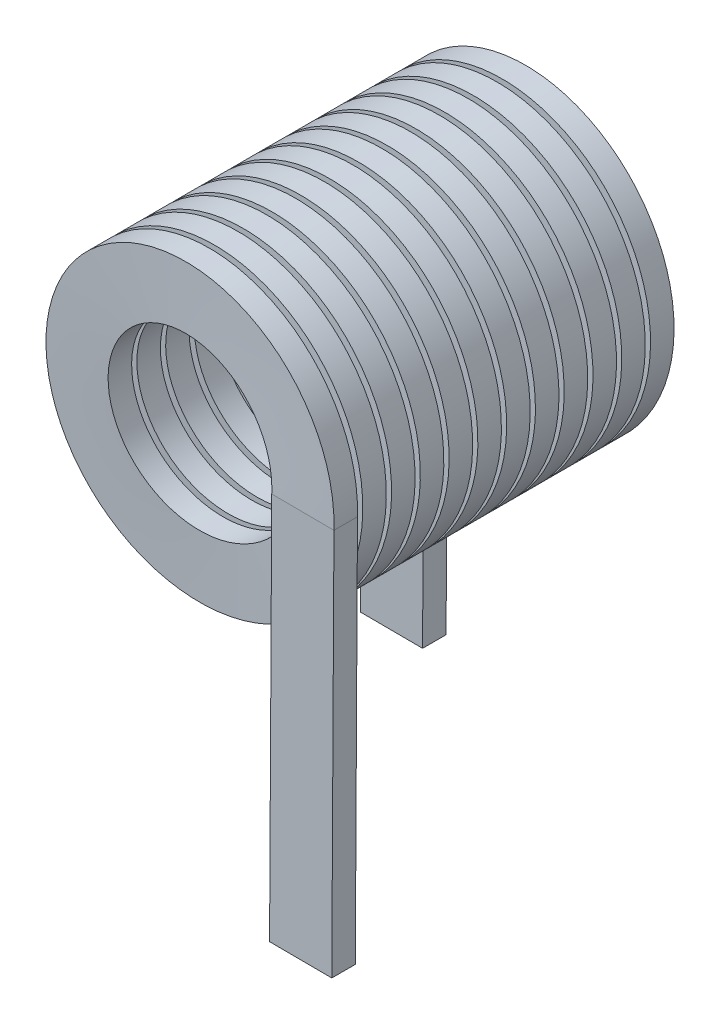
SolidWorks part; units mm, degrees
ref_plane "Front Plane" through (0, 0, 0) normal (0, 0, 1) x (1, 0, 0)
ref_plane "Top Plane" through (0, 0, 0) normal (0, 1, 0) x (1, 0, 0)
ref_plane "Right Plane" through (0, 0, 0) normal (1, 0, 0) x (0, 0, -1)
sketch "Sketch1" plane through (0, 0, 0) normal (0, 0, 1) x (1, 0, 0)
  circle A0 centre (0, 0) radius 15.6845
  dimension "D1" = 31.369
curve "Helix/Spiral1" pitch 3.7592 height 43.2308 turns 11.5
sketch "Sketch6" plane through (0, 0, 0) normal (1, 0, 0) x (0, 0, -1)
  line L0 (-11.0007, 0) -> (53.4115, 0) construction
sketch3d "3DSketch4"
  line L0 (19.7482, 0.0879, 41.6907) -> (19.7482, 0.0879, 44.7641)
  line L1 (19.7482, 0.0879, 44.7641) -> (11.6202, 0.0879, 44.7641)
  line L2 (11.6202, 0.0879, 44.7641) -> (11.6202, 0.0879, 41.6907)
  line L3 (11.6202, 0.0879, 41.6907) -> (19.7482, 0.0879, 41.6907)
  line L4 (15.6842, 0.0879, 43.2274) -> (15.6842, 0.0879, 39.0048) construction
  line L5 (15.6842, 0.0879, 43.2274) -> (20.225, 0.0879, 43.2274) construction
  spline S0 degree 3 poles (-15.6845, 0, 0) (-15.6845, 1.8694, 0.0713) (-15.0016, 5.6424, 0.2153) (-12.0593, 10.5536, 0.4301) (-7.5753, 14.1229, 0.6452) (-2.1228, 15.8847, 0.8603) (3.601, 15.6162, 1.0754) (8.8645, 13.3511, 1.2905) (12.9947, 9.3793, 1.5056) (15.4636, 4.2083, 1.7206) (15.9556, -1.5007, 1.9357) (14.4077, -7.0178, 2.1508) (11.0179, -11.6378, 2.3659) (6.2195, -14.7699, 2.5809) (0.626, -16.0137, 2.796) (-5.0475, -15.2103, 3.0111) (-10.0757, -12.4624, 3.2262) (-13.8159, -8.1212, 3.4413) (-15.7897, -2.7418, 3.6563) (-15.7449, 2.9882, 3.8714) (-13.6872, 8.3361, 4.0865) (-9.8797, 12.6184, 4.3016) (-4.8091, 15.2874, 4.5167) (0.8763, 16.002, 4.7317) (6.4496, 14.6709, 4.9468) (11.1985, 11.4641, 5.1619) (14.5156, 6.7918, 5.377) (15.9771, 1.2511, 5.592) (15.3959, -4.4495, 5.8071) (12.8465, -9.5812, 6.0222) (8.6547, -13.4881, 6.2373) (3.3565, -15.6705, 6.4524) (-2.3709, -15.8496, 6.6674) (-7.7951, -14.0024, 6.8825) (-12.2228, -10.3651, 7.0976) (-15.0878, -5.4027, 7.3127) (-16.024, 0.2505, 7.5278) (-14.9116, 5.8716, 7.7428) (-11.8928, 10.7421, 7.9579) (-7.3536, 14.2392, 8.173) (-1.8743, 15.916, 8.3881) (3.8446, 15.558, 8.6031) (9.072, 13.211, 8.8182) (13.1397, 9.175, 9.0333) (15.5275, 3.9661, 9.2484) (15.9301, -1.7499, 9.4635) (14.2963, -7.2421, 9.6785) (10.8347, -11.8085, 9.8936) (5.9879, -14.8653, 10.1087) (0.3757, -16.0216, 10.3238) (-5.2846, -15.1296, 10.5389) (-10.2693, -12.3034, 10.7539) (-13.9411, -7.9043, 10.969) (-15.8306, -2.4946, 11.1841) (-15.6963, 3.2339, 11.3992) (-13.5553, 8.549, 11.6142) (-9.6813, 12.7712, 11.8293) (-4.5696, 15.3607, 12.0444) (1.1262, 15.9863, 12.2595) (6.6781, 14.5683, 12.4746) (11.3763, 11.2877, 12.6896) (14.62, 6.5641, 12.9047) (15.9947, 1.0013, 13.1198) (15.3245, -4.6895, 13.3349) (12.6952, -9.7808, 13.55) (8.4428, -13.6217, 13.765) (3.1112, -15.7211, 13.9801) (-2.6183, -15.8106, 14.1952) (-8.013, -13.8789, 14.4103) (-12.3833, -10.1728, 14.6253) (-15.1704, -5.1662, 14.8404) (-16.0181, 0.5009, 15.0555) (-14.818, 6.1039, 15.2706) (-11.7235, 10.9266, 15.4857) (-7.1302, 14.3524, 15.7007) (-1.6253, 15.9433, 15.9158) (4.0873, 15.496, 16.1309) (9.2774, 13.0676, 16.346) (13.2815, 8.9685, 16.5611) (15.5875, 3.7229, 16.7761) (15.9009, -1.9986, 16.9912) (14.1813, -7.4647, 17.2063) (10.6488, -11.9764, 17.4214) (5.7549, -14.957, 17.6364) (0.1252, -16.0255, 17.8515) (-5.5204, -15.0452, 18.0666) (-10.4603, -12.1414, 18.2817) (-14.0629, -7.6854, 18.4968) (-15.8677, -2.2469, 18.7118) (-15.6438, 3.4788, 18.9269) (-13.42, 8.7599, 19.142) (-9.4805, 12.921, 19.3571) (-4.329, 15.4302, 19.5722) (1.376, 15.9668, 19.7872) (6.905, 14.4621, 20.0023) (11.5513, 11.1085, 20.2174) (14.7208, 6.3348, 20.4325) (16.0084, 0.7512, 20.6475) (15.2493, -4.9285, 20.8626) (12.5408, -9.978, 21.0777) (8.2289, -13.752, 21.2928) (2.8651, -15.7678, 21.5079) (-2.8651, -15.7678, 21.7229) (-8.2289, -13.752, 21.938) (-12.5408, -9.978, 22.1531) (-15.2493, -4.9285, 22.3682) (-16.0084, 0.7512, 22.5833) (-14.7208, 6.3348, 22.7983) (-11.5513, 11.1085, 23.0134) (-6.905, 14.4621, 23.2285) (-1.376, 15.9668, 23.4436) (4.329, 15.4302, 23.6586) (9.4805, 12.921, 23.8737) (13.42, 8.7599, 24.0888) (15.6438, 3.4788, 24.3039) (15.8677, -2.2469, 24.519) (14.0629, -7.6854, 24.734) (10.4603, -12.1414, 24.9491) (5.5204, -15.0452, 25.1642) (-0.1252, -16.0255, 25.3793) (-5.7549, -14.957, 25.5944) (-10.6488, -11.9764, 25.8094) (-14.1813, -7.4647, 26.0245) (-15.9009, -1.9986, 26.2396) (-15.5875, 3.7229, 26.4547) (-13.2815, 8.9685, 26.6697) (-9.2774, 13.0676, 26.8848) (-4.0873, 15.496, 27.0999) (1.6253, 15.9433, 27.315) (7.1302, 14.3524, 27.5301) (11.7235, 10.9266, 27.7451) (14.818, 6.1039, 27.9602) (16.0181, 0.5009, 28.1753) (15.1704, -5.1662, 28.3904) (12.3833, -10.1728, 28.6055) (8.013, -13.8789, 28.8205) (2.6183, -15.8106, 29.0356) (-3.1112, -15.7211, 29.2507) (-8.4428, -13.6217, 29.4658) (-12.6952, -9.7808, 29.6808) (-15.3245, -4.6895, 29.8959) (-15.9947, 1.0013, 30.111) (-14.62, 6.5641, 30.3261) (-11.3763, 11.2877, 30.5412) (-6.6781, 14.5683, 30.7562) (-1.1262, 15.9863, 30.9713) (4.5696, 15.3607, 31.1864) (9.6813, 12.7712, 31.4015) (13.5553, 8.549, 31.6166) (15.6963, 3.2339, 31.8316) (15.8306, -2.4946, 32.0467) (13.9411, -7.9043, 32.2618) (10.2693, -12.3034, 32.4769) (5.2846, -15.1296, 32.6919) (-0.3757, -16.0216, 32.907) (-5.9879, -14.8653, 33.1221) (-10.8347, -11.8085, 33.3372) (-14.2963, -7.2421, 33.5523) (-15.9301, -1.7499, 33.7673) (-15.5275, 3.9661, 33.9824) (-13.1397, 9.175, 34.1975) (-9.072, 13.211, 34.4126) (-3.8446, 15.558, 34.6277) (1.8743, 15.916, 34.8427) (7.3536, 14.2392, 35.0578) (11.8928, 10.7421, 35.2729) (14.9116, 5.8716, 35.488) (16.024, 0.2505, 35.703) (15.0878, -5.4027, 35.9181) (12.2228, -10.3651, 36.1332) (7.7951, -14.0024, 36.3483) (2.3709, -15.8496, 36.5634) (-3.3565, -15.6705, 36.7784) (-8.6547, -13.4881, 36.9935) (-12.8465, -9.5812, 37.2086) (-15.3959, -4.4495, 37.4237) (-15.9771, 1.2511, 37.6388) (-14.5156, 6.7918, 37.8538) (-11.1985, 11.4641, 38.0689) (-6.4496, 14.6709, 38.284) (-0.8763, 16.002, 38.4991) (4.8091, 15.2874, 38.7141) (9.8797, 12.6184, 38.9292) (13.6872, 8.3361, 39.1443) (15.7449, 2.9882, 39.3594) (15.7897, -2.7418, 39.5745) (13.8159, -8.1212, 39.7895) (10.0757, -12.4624, 40.0046) (5.0475, -15.2103, 40.2197) (-0.626, -16.0137, 40.4348) (-6.2195, -14.7699, 40.6499) (-11.0179, -11.6378, 40.8649) (-14.4077, -7.0178, 41.08) (-15.9556, -1.5007, 41.2951) (-15.4636, 4.2083, 41.5102) (-12.9947, 9.3793, 41.7252) (-8.8645, 13.3511, 41.9403) (-3.601, 15.6162, 42.1554) (2.1228, 15.8847, 42.3705) (7.5753, 14.1229, 42.5856) (12.0593, 10.5536, 42.8007) (15.0016, 5.6424, 43.0155) (15.6845, 1.8694, 43.1595) (15.6845, 0, 43.2308) knots 0 0 0 0 0.004975 0.00995 0.014925 0.0199 0.024876 0.029851 0.034826 0.039801 0.044776 0.049751 0.054726 0.059701 0.064677 0.069652 0.074627 0.079602 0.084577 0.089552 0.094527 0.099502 0.104478 0.109453 0.114428 0.119403 0.124378 0.129353 0.134328 0.139303 0.144279 0.149254 0.154229 0.159204 0.164179 0.169154 0.174129 0.179104 0.18408 0.189055 0.19403 0.199005 0.20398 0.208955 0.21393 0.218905 0.223881 0.228856 0.233831 0.238806 0.243781 0.248756 0.253731 0.258706 0.263682 0.268657 0.273632 0.278607 0.283582 0.288557 0.293532 0.298507 0.303483 0.308458 0.313433 0.318408 0.323383 0.328358 0.333333 0.338308 0.343284 0.348259 0.353234 0.358209 0.363184 0.368159 0.373134 0.378109 0.383085 0.38806 0.393035 0.39801 0.402985 0.40796 0.412935 0.41791 0.422886 0.427861 0.432836 0.437811 0.442786 0.447761 0.452736 0.457711 0.462687 0.467662 0.472637 0.477612 0.482587 0.487562 0.492537 0.497512 0.502488 0.507463 0.512438 0.517413 0.522388 0.527363 0.532338 0.537313 0.542289 0.547264 0.552239 0.557214 0.562189 0.567164 0.572139 0.577114 0.58209 0.587065 0.59204 0.597015 0.60199 0.606965 0.61194 0.616915 0.621891 0.626866 0.631841 0.636816 0.641791 0.646766 0.651741 0.656716 0.661692 0.666667 0.671642 0.676617 0.681592 0.686567 0.691542 0.696517 0.701493 0.706468 0.711443 0.716418 0.721393 0.726368 0.731343 0.736318 0.741294 0.746269 0.751244 0.756219 0.761194 0.766169 0.771144 0.776119 0.781095 0.78607 0.791045 0.79602 0.800995 0.80597 0.810945 0.81592 0.820896 0.825871 0.830846 0.835821 0.840796 0.845771 0.850746 0.855721 0.860697 0.865672 0.870647 0.875622 0.880597 0.885572 0.890547 0.895522 0.900498 0.905473 0.910448 0.915423 0.920398 0.925373 0.930348 0.935323 0.940299 0.945274 0.950249 0.955224 0.960199 0.965174 0.970149 0.975124 0.9801 0.985075 0.99005 0.995025 1 1 1 1 construction
  dimension "D1" = 3.0734
  dimension "D2" = 8.128
sweep "Sweep2" add profiles "3DSketch4" path "Helix/Spiral1"
sketch "Sketch3" plane through (-0.0005, -0.0879, 0) normal (-0.0056, -1, 0) x (1, -0.0056, 0)
  line L4 (-19.7482, -1.5367) -> (-11.6202, -1.5367)
  line L5 (-19.7482, 1.5367) -> (-19.7482, -1.5367)
  line L6 (-11.6202, 1.5367) -> (-19.7482, 1.5367)
  line L7 (-11.6202, -1.5367) -> (-11.6202, 1.5367)
  line L8 (-19.7482, -1.5367) -> (-11.6202, -1.5367)
  line L9 (-19.7482, 1.5367) -> (-19.7482, -1.5367)
  line L10 (-11.6202, 1.5367) -> (-19.7482, 1.5367)
  line L11 (-11.6202, -1.5367) -> (-11.6202, 1.5367)
  dimension "D1" = 0
extrude "Boss-Extrude1" add sketch "Sketch3" along normal blind 50.8
sketch "Sketch4" plane through (0.0005, 0.0879, 0) normal (-0.0056, -1, 0) x (1, -0.0056, 0)
  line L4 (11.6202, 41.6941) -> (19.7482, 41.6941)
  line L5 (11.6202, 44.7675) -> (11.6202, 41.6941)
  line L6 (19.7482, 44.7675) -> (11.6202, 44.7675)
  line L7 (19.7482, 41.6941) -> (19.7482, 44.7675)
  line L8 (11.6202, 41.6941) -> (19.7482, 41.6941)
  line L9 (11.6202, 44.7675) -> (11.6202, 41.6941)
  line L10 (19.7482, 44.7675) -> (11.6202, 44.7675)
  line L11 (19.7482, 41.6941) -> (19.7482, 44.7675)
  dimension "D1" = 0
extrude "Boss-Extrude2" add sketch "Sketch4" along normal blind 50.8
